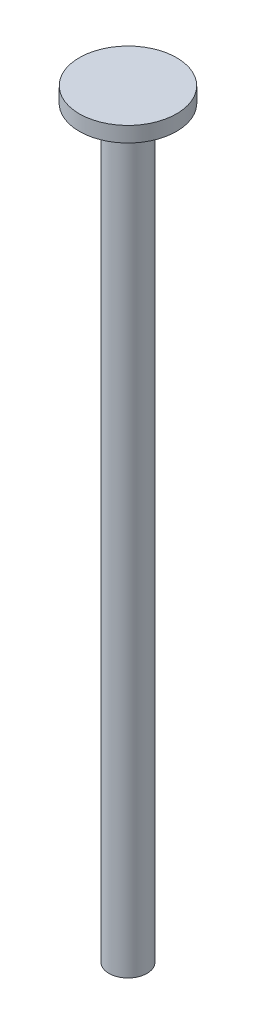
SolidWorks part; units mm, degrees
material "Nylon 101"
ref_plane "Front Plane" through (0, 0, 0) normal (0, 0, 1) x (1, 0, 0)
ref_plane "Top Plane" through (0, 0, 0) normal (0, 1, 0) x (1, 0, 0)
ref_plane "Right Plane" through (0, 0, 0) normal (1, 0, 0) x (0, 0, -1)
sketch "Sketch1" plane through (0, 0, 0) normal (0, 1, 0) x (1, 0, 0)
  circle A0 centre (0, 0) radius 2
  dimension "D1" = 4
extrude "Boss-Extrude1" add sketch "Sketch1" along normal blind 78
sketch "Sketch2" plane through (0, 78, 0) normal (0, 1, 0) x (1, 0, 0)
  circle A0 centre (0, 0) radius 5.1
  dimension "D1" = 10.2
extrude "Boss-Extrude2" add sketch "Sketch2" along normal blind 1.6
